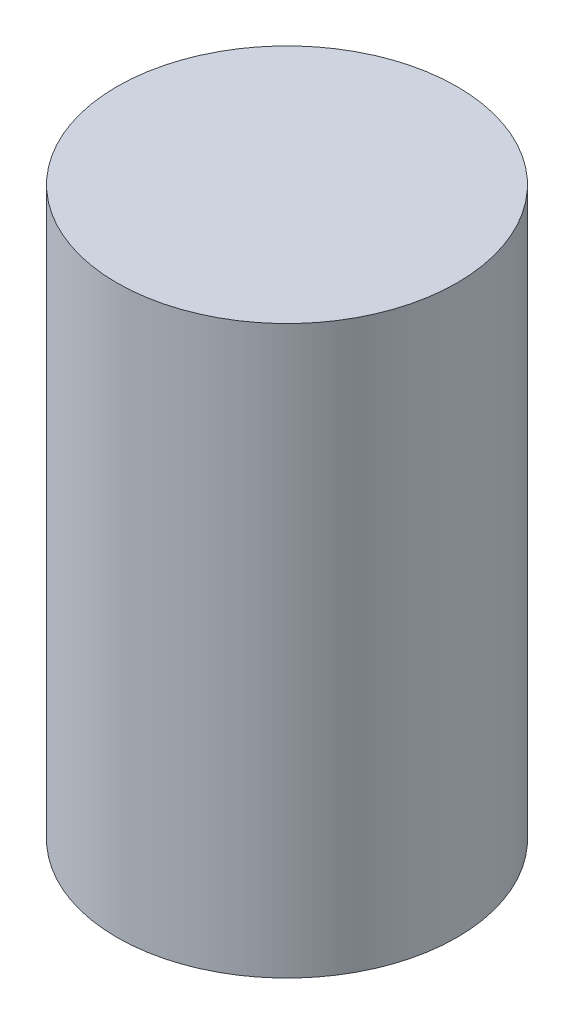
SolidWorks part; units mm, degrees
ref_plane "Front Plane" through (0, 0, 0) normal (0, 0, 1) x (1, 0, 0)
ref_plane "Top Plane" through (0, 0, 0) normal (0, 1, 0) x (1, 0, 0)
ref_plane "Right Plane" through (0, 0, 0) normal (1, 0, 0) x (0, 0, -1)
sketch "Sketch1" plane through (0, 0, 0) normal (0, 1, 0) x (1, 0, 0)
  circle A0 centre (0, 0) radius 38.1
  dimension "D1" = 76.2
extrude "Boss-Extrude1" add sketch "Sketch1" along normal blind 127
